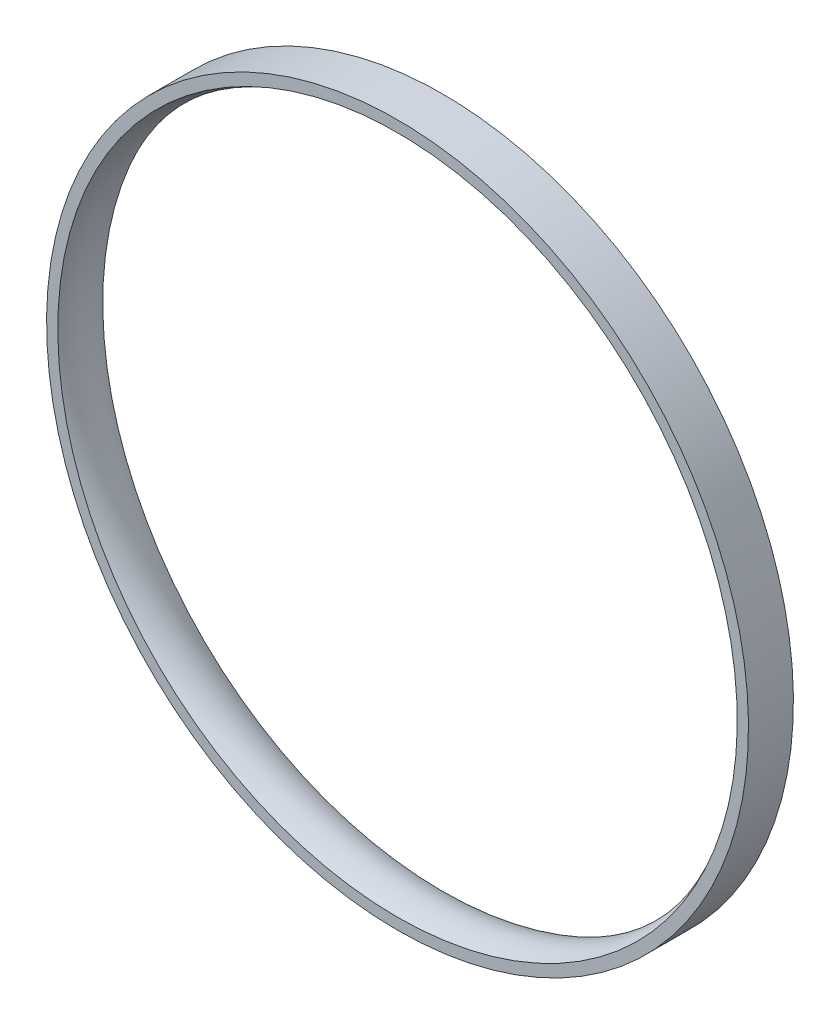
SolidWorks part; units mm, degrees
ref_plane "Plan de face" through (0, 0, 0) normal (0, 0, 1) x (1, 0, 0)
ref_plane "Plan de dessus" through (0, 0, 0) normal (0, 1, 0) x (1, 0, 0)
ref_plane "Plan de droite" through (0, 0, 0) normal (1, 0, 0) x (0, 0, -1)
sketch "Esquisse1" plane through (0, 0, 0) normal (0, 0, 1) x (1, 0, 0)
  circle A0 centre (0, 0) radius 156.15
  dimension "D1" = 312.3
sketch "Esquisse2" plane through (0, 0, 0) normal (1, 0, 0) x (0, 0, -1)
  line L0 (-10, -156.15) -> (10, -156.15)
  line L1 (10, -156.15) -> (10, -151.15)
  line L2 (-10, -156.15) -> (-10, -151.15)
  line L3 (0, 156.15) -> (0, -156.15) construction
  arc A0 (-10, -151.15) -> (10, -151.15) centre (0, -168.4705) cw
  point P3 (0, -156.15)
  point P8 (-10, -150.3431)
  point P9 (10.308, -151.1759)
  point P10 (0, 0)
  dimension "D3" = 20
  dimension "D1" = 20
  dimension "D2" = 5
sweep "Balayage1" add profiles "Esquisse2" path "Esquisse1"
